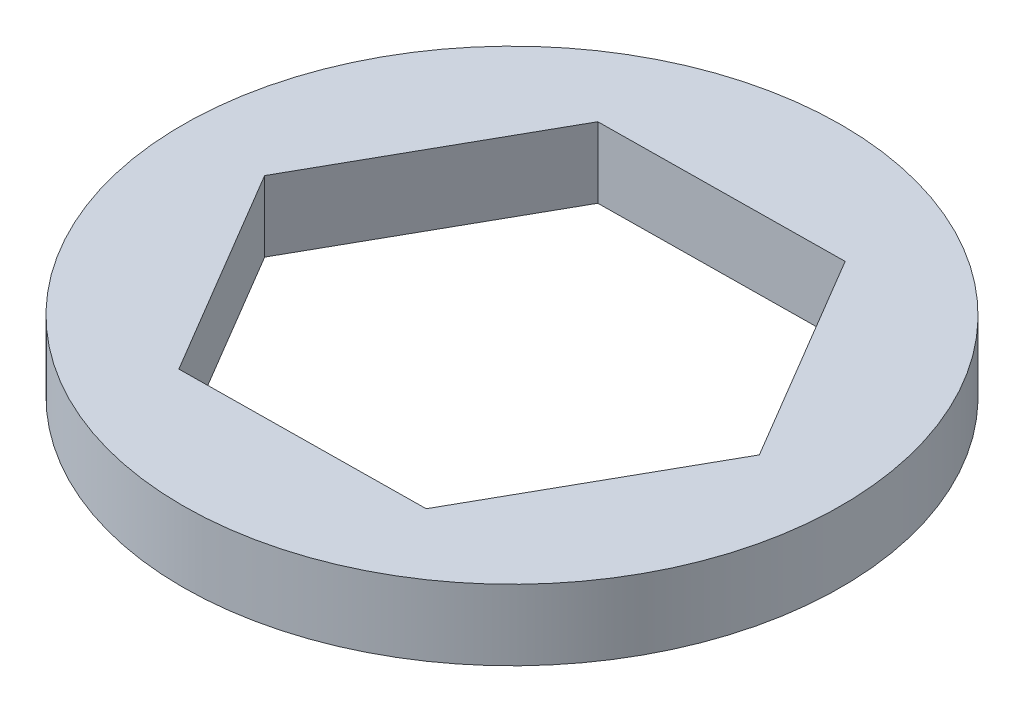
SolidWorks part; units mm, degrees
ref_plane "Front Plane" through (0, 0, 0) normal (0, 0, 1) x (1, 0, 0)
ref_plane "Top Plane" through (0, 0, 0) normal (0, 1, 0) x (1, 0, 0)
ref_plane "Right Plane" through (0, 0, 0) normal (1, 0, 0) x (0, 0, -1)
sketch "Sketch1" plane through (0, 0, 0) normal (0, 1, 0) x (1, 0, 0)
  line L1 (-3.2353, -5.7516) -> (3.3634, -5.6777)
  line L2 (3.3634, -5.6777) -> (6.5987, 0.074)
  line L3 (6.5987, 0.074) -> (3.2353, 5.7516)
  line L4 (3.2353, 5.7516) -> (-3.3634, 5.6777)
  line L5 (-3.3634, 5.6777) -> (-6.5987, -0.074)
  line L6 (-6.5987, -0.074) -> (-3.2353, -5.7516)
  circle A0 centre (0, 0) radius 5.715 construction
  circle A1 centre (0, 0) radius 8.89
extrude "Boss-Extrude1" add sketch "Sketch1" along normal blind 1.905
